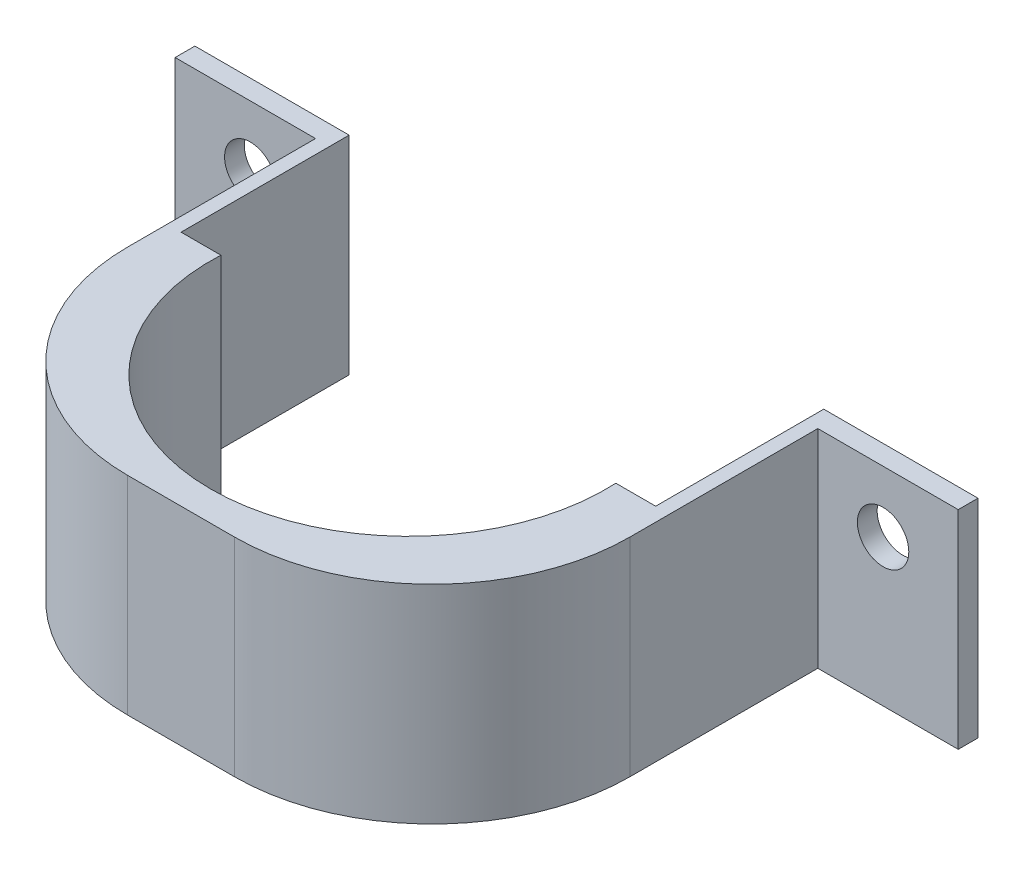
SolidWorks part; units mm, degrees
ref_plane "Front Plane" through (0, 0, 0) normal (0, 0, 1) x (1, 0, 0)
ref_plane "Top Plane" through (0, 0, 0) normal (0, 1, 0) x (1, 0, 0)
ref_plane "Right Plane" through (0, 0, 0) normal (1, 0, 0) x (0, 0, -1)
sketch "Sketch1" plane through (0, 0, 0) normal (0, 0, 1) x (1, 0, 0)
  line L1 (-50.7582, 16.9334) -> (49.8258, 16.9334)
  line L2 (-50.7582, 16.9334) -> (-50.7582, -9.7366)
  line L3 (-50.7582, -9.7366) -> (49.8258, -9.7366)
  line L4 (49.8258, 16.9334) -> (49.8258, -9.7366)
  circle A0 centre (-41.1062, 9.0594) radius 3.302
  circle A1 centre (40.1738, 9.0594) radius 3.302
  dimension "D3" = 6.604
  dimension "D4" = 6.604
  dimension "D1" = 100.584
  dimension "D2" = 26.67
  dimension "D5" = 9.652
  dimension "D6" = 9.652
  dimension "D7" = 7.874
  dimension "D8" = 7.874
extrude "Boss-Extrude1" add sketch "Sketch1" along normal blind 2.54
sketch "Sketch2" plane through (0, 0, 2.54) normal (0, 0, 1) x (1, 0, 0)
  line L0 (49.8258, 16.9334) -> (-50.7582, 16.9334) construction
  line L1 (-32.7242, 16.9334) -> (31.7918, 16.9334)
  line L2 (-32.7242, 16.9334) -> (-32.7242, -9.7366)
  line L3 (-32.7242, -9.7366) -> (31.7918, -9.7366)
  line L4 (31.7918, 16.9334) -> (31.7918, -9.7366)
  line L5 (-50.7582, -9.7366) -> (49.8258, -9.7366) construction
  circle A0 centre (40.1738, 9.0594) radius 3.302 construction
  circle A1 centre (-41.1062, 9.0594) radius 3.302 construction
  dimension "D1" = 8.382
  dimension "D2" = 8.382
extrude "Boss-Extrude2" add sketch "Sketch2" along normal blind 49.53
sketch "Sketch5" plane through (0, -9.7366, 0) normal (0, -1, 0) x (1, 0, 0)
  line L0 (-50.7582, 0) -> (49.8258, 0) construction
  line L1 (-30.9462, 0) -> (30.0138, 0)
  line L2 (-30.9462, 0) -> (-30.9462, 21.59)
  line L3 (-30.9462, 21.59) -> (30.0138, 21.59)
  line L4 (30.0138, 0) -> (30.0138, 21.59)
  line L5 (-32.7242, 52.07) -> (-32.7242, 2.54) construction
  line L6 (31.7918, 52.07) -> (31.7918, 2.54) construction
  circle A0 centre (-0.4662, 22.86) radius 25.4
  line M1 (-50.7582, 0) -> (49.8258, 0)
  dimension "D6" = 50.8
  dimension "D1" = 1.778
  dimension "D2" = 21.59
  dimension "D3" = 1.778
  dimension "D4" = 1.27
  dimension "D5" = 32.258
extrude "Cut-Extrude1" cut sketch "Sketch5" against normal up to next contours L3 A0 | L1 A0 L3 | A0 L3 L2 M1 | A0 L4 L3 M1
fillet "Fillet1" radius 25.4 2 edges at (-32.7242, 3.5984, 52.07) (31.7918, 3.5984, 52.07)
